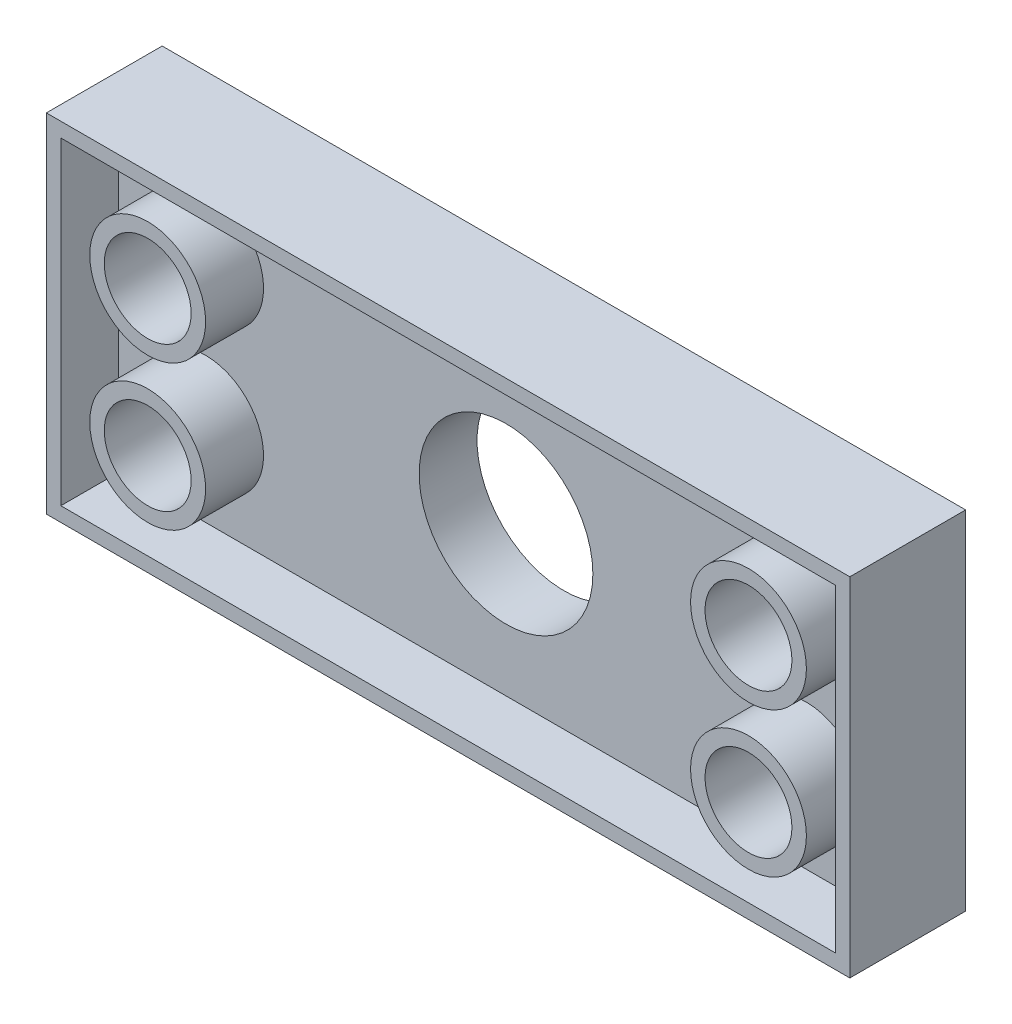
SolidWorks part; units mm, degrees
ref_plane "Front Plane" through (0, 0, 0) normal (0, 0, 1) x (1, 0, 0)
ref_plane "Top Plane" through (0, 0, 0) normal (0, 1, 0) x (1, 0, 0)
ref_plane "Right Plane" through (0, 0, 0) normal (1, 0, 0) x (0, 0, -1)
sketch "Sketch1" plane through (0, 0, 0) normal (0, 0, 1) x (1, 0, 0)
  line L0 (-3.9673, 145.5007) -> (96.0327, 145.5007) construction
  line L1 (96.0327, 145.5007) -> (102.3827, 145.5007) construction
  line L2 (102.3827, 145.5007) -> (121.4327, 145.5007) construction
  line L3 (111.9077, 145.5007) -> (111.9077, 113.7507) construction
  line L5 (46.0327, 185.2083) -> (46.0327, 69.5324) construction
  line L6 (-29.3673, 145.5007) -> (-73.3444, 145.5007) construction
  line L7 (-19.8423, 145.5007) -> (-19.8423, 113.7507) construction
  line L8 (-10.3173, 145.5007) -> (-29.3673, 145.5007) construction
  line L9 (-3.9673, 145.5007) -> (-10.3173, 145.5007) construction
  line L11 (130.9577, 164.5507) -> (-38.8923, 164.5507)
  line L12 (130.9577, 164.5507) -> (130.9577, 94.7007)
  line L13 (130.9577, 94.7007) -> (-38.8923, 94.7007)
  line L14 (-38.8923, 164.5507) -> (-38.8923, 94.7007)
  circle A0 centre (-19.8423, 145.5007) radius 9.525
  circle A1 centre (-19.8423, 113.7507) radius 9.525
  circle A2 centre (111.9077, 145.5007) radius 9.525
  circle A3 centre (111.9077, 113.7507) radius 9.525
  circle A4 centre (46.0327, 127.3703) radius 19.05
  point P15 (46.0327, 145.5007)
  dimension "D6" = 19.05
  dimension "D10" = 38.1
  dimension "D1" = 50
  dimension "D2" = 6.35
  dimension "D3" = 19.05
  dimension "D4" = 19.05
  dimension "D5" = 31.75
  dimension "D7" = 19.05
  dimension "D8" = 19.05
  dimension "D9" = 19.05
extrude "Boss-Extrude1" add sketch "Sketch1" along normal blind 12.7
sketch "Sketch2" plane through (0, 0, 12.7) normal (0, 0, 1) x (1, 0, 0)
  circle A0 centre (111.9077, 145.5007) radius 9.525 construction
  circle A1 centre (111.9077, 113.7507) radius 9.525 construction
  circle A2 centre (-19.8423, 113.7507) radius 9.525 construction
  circle A3 centre (-19.8423, 145.5007) radius 9.525 construction
  circle A4 centre (111.9077, 145.5007) radius 9.525
  circle A5 centre (111.9077, 113.7507) radius 9.525
  circle A6 centre (-19.8423, 113.7507) radius 9.525
  circle A7 centre (-19.8423, 145.5007) radius 9.525
  circle A8 centre (111.9077, 145.5007) radius 12.7
  circle A9 centre (111.9077, 113.7507) radius 12.7
  circle A10 centre (-19.8423, 113.7507) radius 12.7
  circle A11 centre (-19.8423, 145.5007) radius 12.7
  dimension "D1" = 3.175
extrude "Boss-Extrude2" add sketch "Sketch2" along normal blind 12.7
sketch "Sketch3" plane through (0, 0, 0) normal (0, 0, -1) x (-1, 0, 0)
  line L0 (38.8923, 164.5507) -> (38.8923, 94.7007) construction
  line L1 (38.8923, 94.7007) -> (-130.9577, 94.7007) construction
  line L2 (-130.9577, 94.7007) -> (-130.9577, 164.5507) construction
  line L3 (-130.9577, 164.5507) -> (38.8923, 164.5507) construction
  line L4 (38.8923, 164.5507) -> (38.8923, 94.7007)
  line L5 (38.8923, 94.7007) -> (-130.9577, 94.7007)
  line L6 (-130.9577, 94.7007) -> (-130.9577, 164.5507)
  line L7 (-130.9577, 164.5507) -> (38.8923, 164.5507)
  line L8 (42.0673, 167.7257) -> (42.0673, 91.5257)
  line L9 (42.0673, 91.5257) -> (-134.1327, 91.5257)
  line L10 (-134.1327, 91.5257) -> (-134.1327, 167.7257)
  line L11 (-134.1327, 167.7257) -> (42.0673, 167.7257)
  dimension "D1" = 3.175
extrude "Boss-Extrude3" add sketch "Sketch3" against normal blind 25.4
